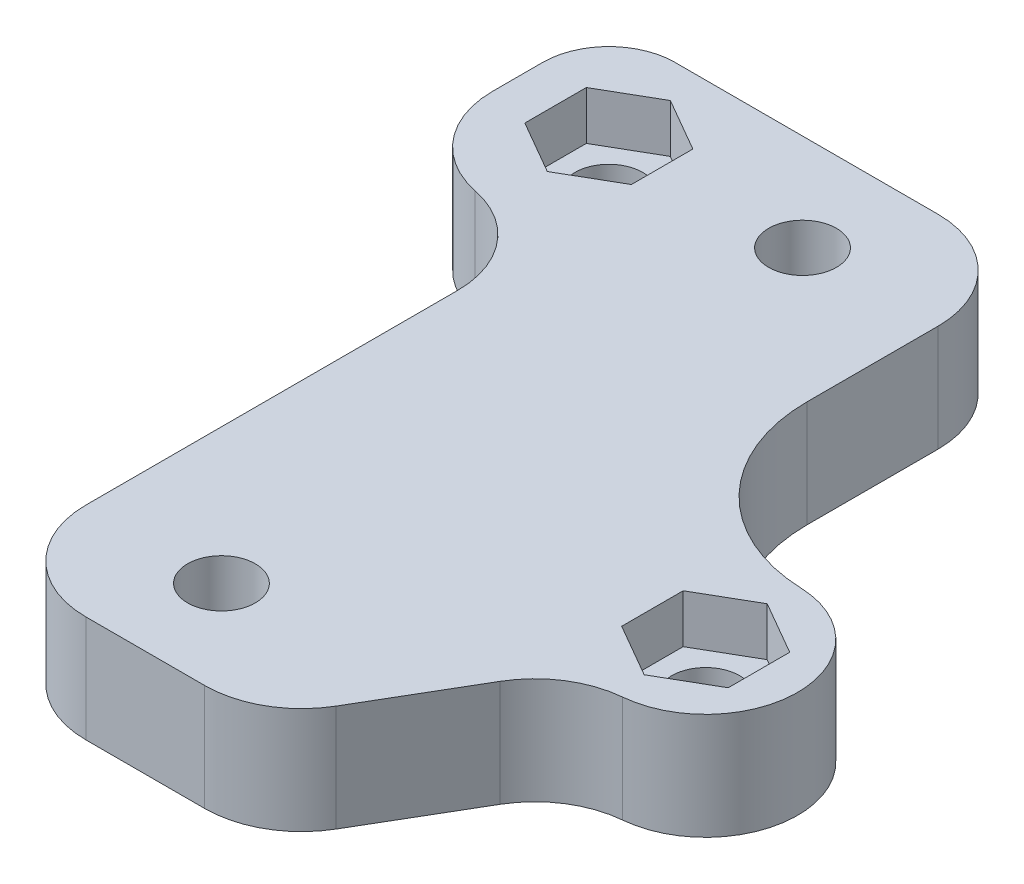
SolidWorks part; units mm, degrees
material "ABS PC"
ref_plane "Front Plane" through (0, 0, 0) normal (0, 0, 1) x (1, 0, 0)
ref_plane "Top Plane" through (0, 0, 0) normal (0, 1, 0) x (1, 0, 0)
ref_plane "Right Plane" through (0, 0, 0) normal (1, 0, 0) x (0, 0, -1)
sketch "Sketch2" plane through (0, 0, 0) normal (0, 1, 0) x (1, 0, 0)
  line L0 (0, 0) -> (35, 0)
  line L1 (0, 0) -> (0, 40)
  line L2 (35, 0) -> (35, 40)
  line L3 (0, 40) -> (35, 40)
  circle A0 centre (5, 35) radius 1.75
  circle A1 centre (30, 15) radius 1.75
  circle A6 centre (15, 35) radius 1.75
  circle A7 centre (15, 5) radius 1.75
  dimension "D3" = 3.5
  dimension "D4" = 25
  dimension "D5" = 20
  dimension "D6" = 5
  dimension "D7" = 5
  dimension "D8" = 35
  dimension "D2" = 40
  dimension "D13" = 10
  dimension "D14" = 5
extrude "Boss-Extrude2" add sketch "Sketch2" along normal blind 5.5
sketch "Sketch3" plane through (0, 0, 0) normal (0, -1, 0) x (1, 0, 0)
  line L1 (7.75, -36.5877) -> (7.75, -33.4123)
  line L2 (7.75, -33.4123) -> (5, -31.8246)
  line L3 (5, -31.8246) -> (2.25, -33.4123)
  line L4 (2.25, -33.4123) -> (2.25, -36.5877)
  line L5 (2.25, -36.5877) -> (5, -38.1754)
  line L6 (5, -38.1754) -> (7.75, -36.5877)
  line L7 (30, -11.8246) -> (27.25, -13.4123)
  line L8 (27.25, -13.4123) -> (27.25, -16.5877)
  line L9 (27.25, -16.5877) -> (30, -18.1754)
  line L10 (30, -18.1754) -> (32.75, -16.5877)
  line L11 (32.75, -16.5877) -> (32.75, -13.4123)
  line L12 (32.75, -13.4123) -> (30, -11.8246)
  circle A0 centre (5, -35) radius 2.75 construction
  circle A2 centre (30, -15) radius 2.75 construction
  circle A3 centre (5, -35) radius 1.75 construction
  dimension "D1" = 5.5
extrude "Cut-Extrude1" cut sketch "Sketch3" against normal up to next from offset 3 offset against normal yes
sketch "Sketch4" plane through (0, 5.5, 0) normal (0, 1, 0) x (1, 0, 0)
  line L1 (17.75, 36.5877) -> (15, 38.1754)
  line L2 (15, 38.1754) -> (12.25, 36.5877)
  line L3 (12.25, 36.5877) -> (12.25, 33.4123)
  line L4 (12.25, 33.4123) -> (15, 31.8246)
  line L5 (15, 31.8246) -> (17.75, 33.4123)
  line L6 (17.75, 33.4123) -> (17.75, 36.5877)
  line L7 (13.4123, 7.75) -> (11.8246, 5)
  line L8 (11.8246, 5) -> (13.4123, 2.25)
  line L9 (13.4123, 2.25) -> (16.5877, 2.25)
  line L10 (16.5877, 2.25) -> (18.1754, 5)
  line L11 (18.1754, 5) -> (16.5877, 7.75)
  line L12 (16.5877, 7.75) -> (13.4123, 7.75)
  circle A0 centre (15, 35) radius 2.75 construction
  circle A1 centre (15, 5) radius 2.75 construction
  dimension "D1" = 5.5
extrude "Cut-Extrude2" cut sketch "Sketch4" against normal blind 10 from offset 3 offset against normal yes
sketch "Sketch5" plane through (0, 5.5, 0) normal (0, 1, 0) x (1, 0, 0)
  line L0 (0, 36.5877) -> (0, 40)
  line L1 (0, 40) -> (0, 0) construction
  line L2 (0, 40) -> (3.4123, 40)
  line L3 (35, 40) -> (0, 40) construction
  line L5 (30, 19.75) -> (22, 19.75)
  line L6 (22, 19.75) -> (22, 40)
  line L7 (22, 40) -> (35, 40)
  line L8 (35, 40) -> (35, 0)
  line L9 (35, 0) -> (22, 0)
  line L10 (0, 0) -> (35, 0) construction
  line L11 (30, 10.25) -> (28, 10.25)
  line L12 (28, 10.25) -> (22, 0)
  line L13 (0, 34) -> (0, 0)
  line L14 (0, 0) -> (8, 0)
  line L15 (8, 0) -> (8, 29)
  line L16 (8, 29) -> (5, 29)
  arc A0 (0, 36.5877) -> (3.4123, 40) centre (3.4123, 36.5877) cw
  arc A1 (30, 19.75) -> (30, 10.25) centre (30, 15) cw
  circle A2 centre (30, 15) radius 1.75 construction
  circle A3 centre (15, 5) radius 1.75 construction
  arc A5 (0, 34) -> (5, 29) centre (5, 34) ccw
  circle A7 centre (5, 35) radius 1.75 construction
  dimension "D1" = 4.75
  dimension "D5" = 6
  dimension "D2" = 7
  dimension "D3" = 9.5
  dimension "D4" = 2
  dimension "D6" = 5
  dimension "D7" = 7
extrude "Cut-Extrude3" cut sketch "Sketch5" against normal through all
fillet "Fillet3" radius 5 5 edges at (28, 2.75, -10.25) (22, 2.75, 0) (22, 2.75, -40) (8, 2.75, -29) (8, 2.75, 0)
fillet "Fillet4" radius 8.5 1 edges at (22, 2.75, -19.75)
